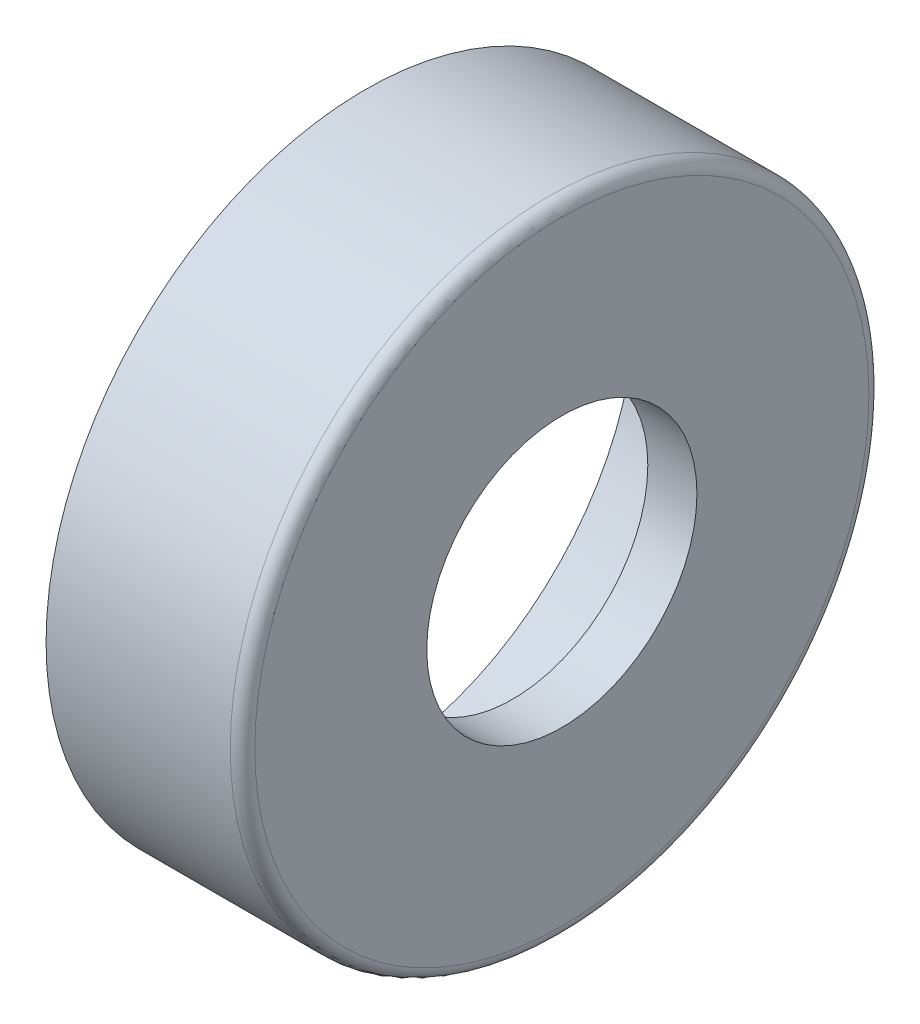
SolidWorks part; units mm, degrees
ref_plane "Plan de face" through (0, 0, 0) normal (0, 0, 1) x (1, 0, 0)
ref_plane "Plan de dessus" through (0, 0, 0) normal (0, 1, 0) x (1, 0, 0)
ref_plane "Plan de droite" through (0, 0, 0) normal (1, 0, 0) x (0, 0, -1)
sketch "Esquisse1" plane through (0, 0, 0) normal (0, 0, 1) x (1, 0, 0)
  line L0 (-12.9863, 0) -> (14.6062, 0) construction
  line L1 (-3.5, 13) -> (4.5, 13)
  line L2 (-3.5, 13) -> (-3.5, 11)
  line L3 (-3.5, 11) -> (0, 11)
  line L4 (4.5, 13) -> (4.5, 5.5)
  line L5 (2.5, 5.5) -> (4.5, 5.5)
  line L6 (2.5, 5.5) -> (2.5, 8.5)
  arc A0 (2.5, 8.5) -> (0, 11) centre (0, 8.5) ccw
  dimension "D1" = 5
  dimension "D2" = 17
  dimension "D3" = 26
  dimension "D4" = 8
  dimension "D5" = 11
  dimension "D6" = 2
revolve "Révolution1" add sketch "Esquisse1" angle 360 about L0
fillet "Congé1" radius 0.5 1 edges at (4.5, 0, 13)
